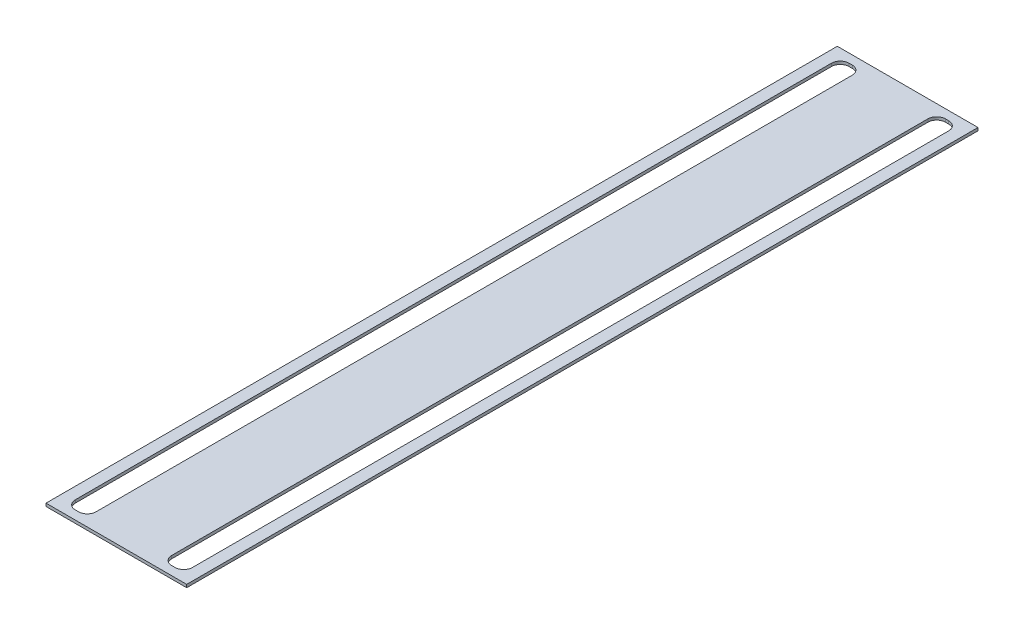
SolidWorks part; units mm, degrees
material "Silicon Rubber"
ref_plane "Front Plane" through (0, 0, 0) normal (0, 0, 1) x (1, 0, 0)
ref_plane "Top Plane" through (0, 0, 0) normal (0, 1, 0) x (1, 0, 0)
ref_plane "Right Plane" through (0, 0, 0) normal (1, 0, 0) x (0, 0, -1)
sketch "Sketch1" plane through (0, 0, 0) normal (0, 1, 0) x (1, 0, 0)
  line L0 (0, 0) -> (-12.9, 0) construction
  line L1 (-20, 132) -> (-12.9, 132)
  line L2 (-20, 132) -> (-20, -132)
  line L3 (-20, -132) -> (-12.9, -132)
  line L4 (-12.9, 132) -> (-12.9, -132)
  line L9 (24, -135) -> (-24, -135)
  line L10 (24, -135) -> (24, 135)
  line L11 (24, 135) -> (-24, 135)
  line L12 (-24, -135) -> (-24, 135)
  line L13 (24, -135) -> (-24, 135) construction
  line L14 (24, 135) -> (-24, -135) construction
  line L15 (0, 0) -> (0, 77.4276) construction
  line L16 (20, -132) -> (12.9, -132)
  line L17 (12.9, 132) -> (12.9, -132)
  line L18 (20, 132) -> (12.9, 132)
  line L19 (20, 132) -> (20, -132)
  point P8 (0, 0)
  dimension "D1" = 7.1
  dimension "D2" = 12.9
  dimension "D3" = 264
  dimension "D4" = 3
  dimension "D5" = 4
extrude "Boss-Extrude1" add sketch "Sketch1" along normal blind 1
fillet "Fillet1" radius 3 8 edges at (12.9, 0.5, -132) (12.9, 0.5, 132) (20, 0.5, 132) (-12.9, 0.5, 132) (-12.9, 0.5, -132) (-20, 0.5, -132) (-20, 0.5, 132) (20, 0.5, -132)
